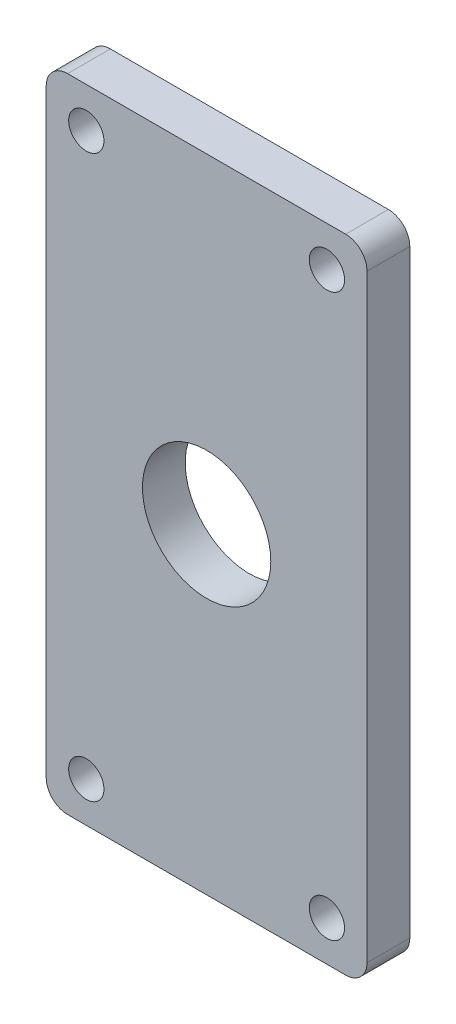
SolidWorks part; units mm, degrees
ref_plane "前视基准面" through (0, 0, 0) normal (0, 0, 1) x (1, 0, 0)
ref_plane "上视基准面" through (0, 0, 0) normal (0, 1, 0) x (1, 0, 0)
ref_plane "右视基准面" through (0, 0, 0) normal (1, 0, 0) x (0, 0, -1)
sketch "草图6" plane through (0, 0, 0) normal (0, 0, 1) x (1, 0, 0)
  line L0 (-7.5, 30) -> (-15, 22.5) construction
  line L1 (-15, -30) -> (15, -30)
  line L2 (-15, -30) -> (-15, 30)
  line L3 (-15, 30) -> (15, 30)
  line L4 (15, -30) -> (15, 30)
  line L7 (-15, 30) -> (-7.5, 30)
  line L8 (-15, 30) -> (-15, 22.5)
  line L9 (-15, 22.5) -> (-7.5, 22.5) construction
  line L10 (-7.5, 30) -> (-7.5, 22.5) construction
  line L11 (15, 30) -> (7.5, 30)
  line L12 (15, 30) -> (15, 22.5)
  line L13 (15, 22.5) -> (7.5, 22.5) construction
  line L14 (7.5, 30) -> (7.5, 22.5) construction
  line L15 (-15, -30) -> (-7.5, -30)
  line L16 (-15, -30) -> (-15, -22.5)
  line L17 (-15, -22.5) -> (-7.5, -22.5) construction
  line L18 (-7.5, -30) -> (-7.5, -22.5) construction
  line L19 (15, -30) -> (7.5, -30)
  line L20 (15, -30) -> (15, -22.5)
  line L21 (15, -22.5) -> (7.5, -22.5) construction
  line L22 (7.5, -30) -> (7.5, -22.5) construction
  line L23 (7.5, 30) -> (15, 22.5) construction
  line L24 (-15, -22.5) -> (-7.5, -30) construction
  line L25 (15, -22.5) -> (7.5, -30) construction
  circle A0 centre (0, 0) radius 6
  point P0 (0, 0)
extrude "凸台-拉伸4" add sketch "草图6" along normal blind 4
fillet "圆角2" radius 2 1 edges at (15, 30, 2)
fillet "圆角6" radius 2 1 edges at (15, -30, 2)
fillet "圆角12" radius 2 1 edges at (-15, 30, 2)
fillet "圆角16" radius 2 1 edges at (-15, -30, 2)
hole_wizard "M4 螺纹孔1" positions "草图9" profile "草图10" tap size "M4" standard "GB" end condition through all
sketch "草图9" plane through (0, 0, 4) normal (0, 0, 1) x (1, 0, 0)
  line L0 (-7.5, 30) -> (-15, 22.5) construction
  line L1 (7.5, 30) -> (15, 22.5) construction
  line L2 (15, -22.5) -> (7.5, -30) construction
  line L3 (-15, -22.5) -> (-7.5, -30) construction
  point P0 (-11.25, 26.25)
  point P4 (11.25, 26.25)
  point P8 (11.25, -26.25)
  point P12 (-11.25, -26.25)
sketch "草图10" plane through (-11.25, 26.25, 4) normal (1, 0, 0) x (0, -1, 0)
  line L0 (0, 0) -> (0, 4)
  line L1 (0, 4) -> (1.65, 4)
  line L2 (1.65, 4) -> (1.65, 0)
  line L5 (1.65, 0) -> (0, 0)
  line L11 (0, -6.35) -> (0, 107.95) construction
  dimension "通孔螺纹孔钻头直径" = 3.3
  dimension "通孔螺纹孔钻头深度" = 4
cosmetic thread "孔螺蚊线1" parameters "D2"=4
cosmetic thread "孔螺蚊线2" parameters "D2"=4
cosmetic thread "孔螺蚊线3" parameters "D2"=4
cosmetic thread "孔螺蚊线4" parameters "D2"=4
